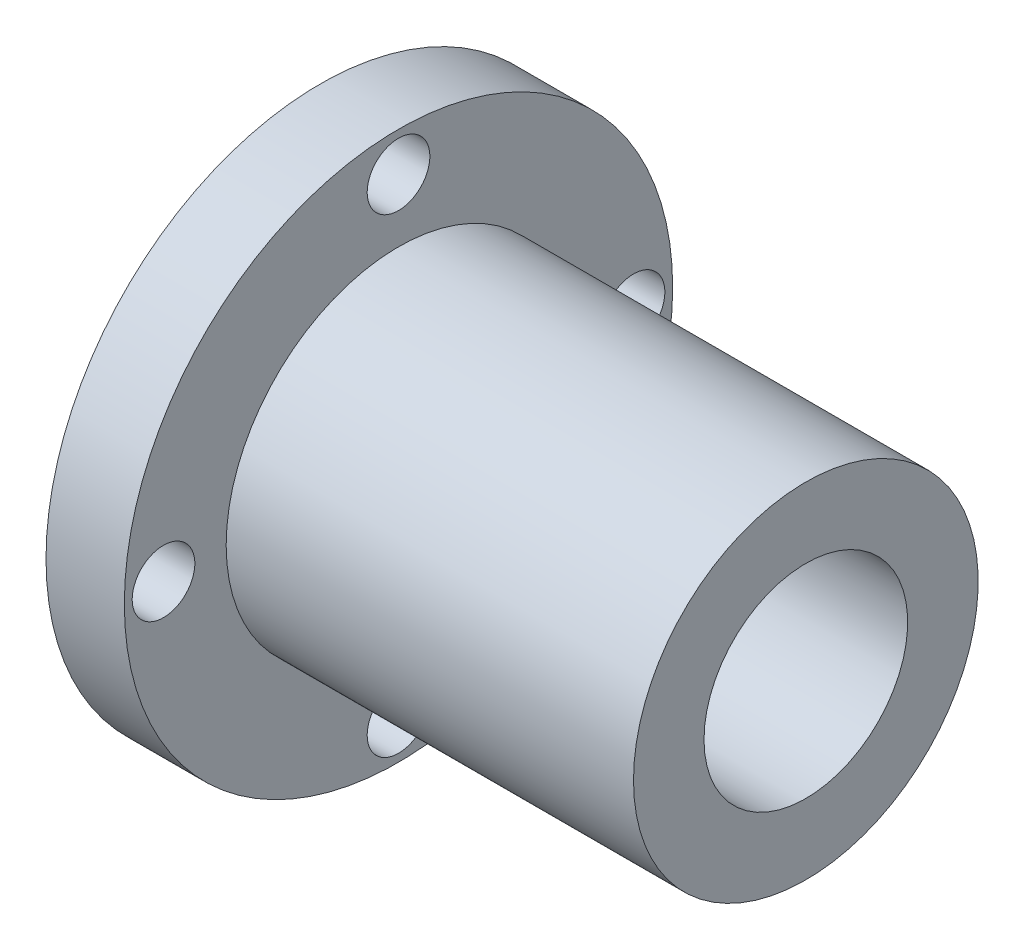
SolidWorks part; units mm, degrees
ref_plane "Plan de face" through (0, 0, 0) normal (0, 0, 1) x (1, 0, 0)
ref_plane "Plan de dessus" through (0, 0, 0) normal (0, 1, 0) x (1, 0, 0)
ref_plane "Plan de droite" through (0, 0, 0) normal (1, 0, 0) x (0, 0, -1)
sketch "Esquisse1" plane through (0, 0, 0) normal (0, 0, 1) x (1, 0, 0)
  line L0 (0, 10) -> (0, 17.5)
  line L1 (0, 17.5) -> (5, 17.5)
  line L2 (5, 17.5) -> (5, 11)
  line L3 (20, 6.5) -> (20, 10)
  line L4 (20, 6.5) -> (31, 6.5)
  line L5 (0, 10) -> (20, 10)
  line L6 (5, 11) -> (31, 11)
  line L7 (31, 6.5) -> (31, 11)
  line L8 (0, 0) -> (34.6007, 0) construction
revolve "Révolution1" add sketch "Esquisse1" angle 360 about L8
sketch "Esquisse2" plane through (0, 0, 0) normal (-1, 0, 0) x (0, 0, 1)
  circle A1 centre (0, 15) radius 2
  circle A2 centre (15, 0) radius 2
  circle A3 centre (0, -15) radius 2
  circle A4 centre (-15, 0) radius 2
extrude "Extrusion1" cut sketch "Esquisse2" against normal through all
